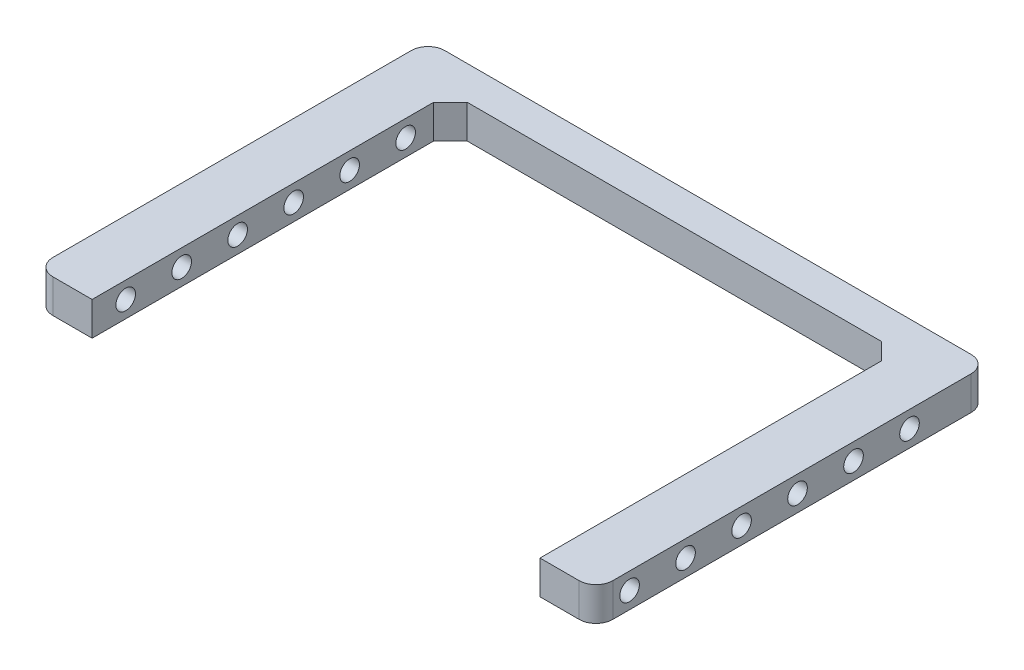
SolidWorks part; units mm, degrees
ref_plane "Front" through (0, 0, 0) normal (0, 0, 1) x (1, 0, 0)
ref_plane "Top" through (0, 0, 0) normal (0, 1, 0) x (1, 0, 0)
ref_plane "Right" through (0, 0, 0) normal (1, 0, 0) x (0, 0, -1)
sketch "Sketch1" plane through (0, 0, 0) normal (0, 1, 0) x (1, 0, 0)
  line L0 (-25, -21) -> (-20, -21)
  line L1 (-25, -21) -> (25, -21) construction
  line L2 (-25, -21) -> (-25, 14)
  line L3 (-25, 14) -> (25, 14)
  line L4 (25, -21) -> (25, 14)
  line L5 (-25, -21) -> (25, 14) construction
  line L6 (-25, 14) -> (25, -21) construction
  line L7 (-20, -21) -> (-20, 11)
  line L8 (-20, 11) -> (20, 11)
  line L9 (20, 11) -> (20, -21)
  line L10 (20, -21) -> (25, -21)
  line L12 (0, 0) -> (0, 11) construction
  point P0 (0, -3.5)
  dimension "D1" = 40
  dimension "D2" = 32
  dimension "D3" = 3
  dimension "D4" = 5
  dimension "D5" = 5
  dimension "D6" = 11
extrude "Boss-Extrude1" add sketch "Sketch1" along normal blind 3
sketch "Sketch2" plane through (25, 0, 0) normal (-1, 0, 0) x (0, 0, 1)
  line L0 (21, 1.5) -> (18, 1.5) construction
  line L1 (21, 3) -> (21, 0) construction
  line L2 (18, 1.5) -> (13, 1.5) construction
  circle A0 centre (18, 1.5) radius 0.875
  circle A1 centre (13, 1.5) radius 0.875
  circle A2 centre (8, 1.5) radius 0.875
  circle A3 centre (3, 1.5) radius 0.875
  circle A4 centre (-2, 1.5) radius 0.875
  circle A5 centre (-7, 1.5) radius 0.875
  dimension "D1" = 1.75
  dimension "D2" = 3
  dimension "D4" = 5
  dimension "D3" = 6
extrude "Cut-Extrude1" cut sketch "Sketch2" against normal blind 3 and the other way through all
fillet "Fillet2" radius 1.5 4 edges at (-25, 1.5, -14) (-25, 1.5, 21) (25, 1.5, -14) (25, 1.5, 21)
chamfer "Chamfer1" distance 1.5 angle 45 2 edges at (-20, 1.5, -11) (20, 1.5, -11)
move or copy body "Body-Move/Copy1" [suppressed] bodies to move or copy 104
